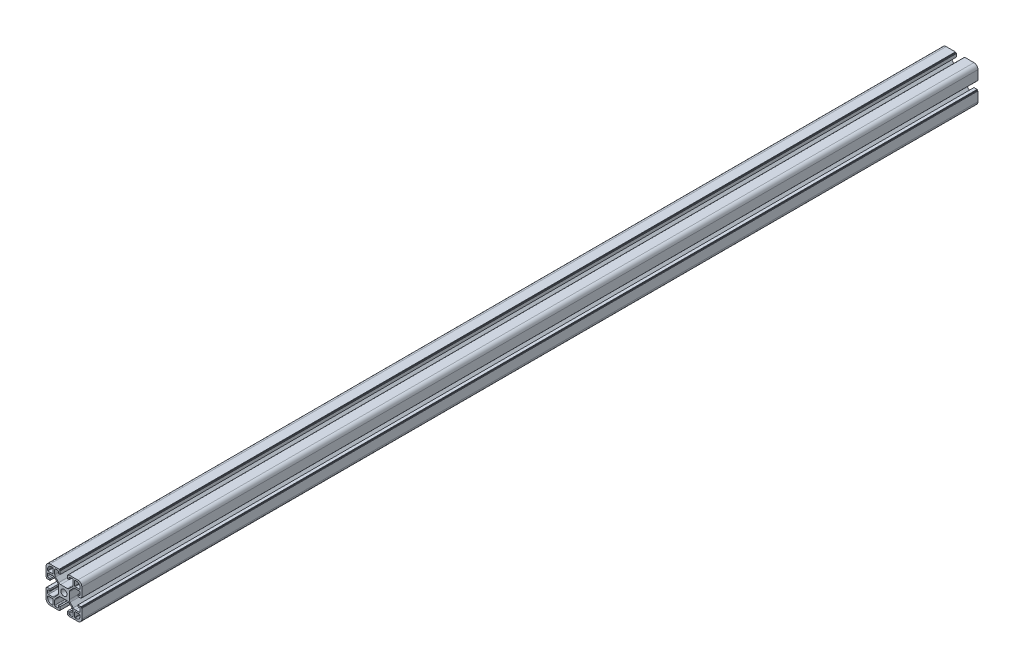
SolidWorks part; units mm, degrees
ref_plane "Front Plane" through (0, 0, 0) normal (0, 0, 1) x (1, 0, 0)
ref_plane "Top Plane" through (0, 0, 0) normal (0, 1, 0) x (1, 0, 0)
ref_plane "Right Plane" through (0, 0, 0) normal (1, 0, 0) x (0, 0, -1)
sketch "Sketch1" plane through (0, 0, 0) normal (0, 0, 1) x (1, 0, 0)
  line L0 (84.1702, 31.7204) -> (84.1702, 42.1204)
  line L1 (44.1702, 62.7204) -> (44.1702, 52.3204)
  line L2 (48.6702, 27.2204) -> (59.0702, 27.2204)
  line L3 (79.6702, 67.2204) -> (69.4702, 67.2204)
  line L4 (84.1702, 52.3204) -> (84.1702, 62.7204)
  line L5 (58.8702, 67.2204) -> (48.6702, 67.2204)
  line L6 (44.1702, 42.1204) -> (44.1702, 31.7204)
  line L7 (69.2702, 27.2204) -> (79.6702, 27.2204)
  line L10 (44.1702, 42.1204) -> (44.7702, 42.1204)
  line L11 (44.9702, 42.3204) -> (44.9702, 42.9204)
  line L12 (48.6702, 43.1204) -> (45.1702, 43.1204)
  line L13 (48.6702, 41.3204) -> (48.6702, 43.1204)
  line L14 (46.9702, 41.3204) -> (48.6702, 41.3204)
  line L15 (45.9702, 37.9704) -> (45.9702, 40.3204)
  line L16 (51.6169, 36.9704) -> (46.9702, 36.9704)
  line L17 (57.2915, 41.4024) -> (53.7382, 37.8491)
  line L18 (58.1702, 50.9171) -> (58.1702, 43.5237)
  line L19 (53.7382, 56.5917) -> (57.2915, 53.0384)
  line L20 (46.9702, 57.4704) -> (51.6169, 57.4704)
  line L21 (45.9702, 54.1204) -> (45.9702, 56.4704)
  line L22 (48.6702, 53.1204) -> (46.9702, 53.1204)
  line L23 (48.6702, 51.3204) -> (48.6702, 53.1204)
  line L24 (45.1702, 51.3204) -> (48.6702, 51.3204)
  line L25 (44.9702, 51.5204) -> (44.9702, 52.1204)
  line L26 (44.7702, 52.3204) -> (44.1702, 52.3204)
  line L29 (59.0702, 67.0204) -> (59.0702, 66.6204)
  line L30 (59.2702, 66.4204) -> (59.8702, 66.4204)
  line L31 (60.0702, 62.7204) -> (60.0702, 66.2204)
  line L32 (58.2702, 62.7204) -> (60.0702, 62.7204)
  line L33 (58.2702, 64.4204) -> (58.2702, 62.7204)
  line L34 (54.9202, 65.4204) -> (57.2702, 65.4204)
  line L35 (53.9202, 59.7737) -> (53.9202, 64.4204)
  line L36 (58.3522, 54.0991) -> (54.7989, 57.6524)
  line L37 (67.8669, 53.2204) -> (60.4735, 53.2204)
  line L38 (73.5415, 57.6524) -> (69.9882, 54.0991)
  line L39 (74.4202, 64.4204) -> (74.4202, 59.7737)
  line L40 (71.0702, 65.4204) -> (73.4202, 65.4204)
  line L41 (70.0702, 62.7204) -> (70.0702, 64.4204)
  line L42 (68.2702, 62.7204) -> (70.0702, 62.7204)
  line L43 (68.2702, 66.2204) -> (68.2702, 62.7204)
  line L44 (68.4702, 66.4204) -> (69.0702, 66.4204)
  line L45 (69.2702, 66.6204) -> (69.2702, 67.0204)
  line L48 (84.1702, 52.3204) -> (83.5702, 52.3204)
  line L49 (83.3702, 52.1204) -> (83.3702, 51.5204)
  line L50 (79.6702, 51.3204) -> (83.1702, 51.3204)
  line L51 (79.6702, 53.1204) -> (79.6702, 51.3204)
  line L52 (81.3702, 53.1204) -> (79.6702, 53.1204)
  line L53 (82.3702, 56.4704) -> (82.3702, 54.1204)
  line L54 (76.7235, 57.4704) -> (81.3702, 57.4704)
  line L55 (71.0489, 53.0384) -> (74.6022, 56.5917)
  line L56 (70.1702, 43.5237) -> (70.1702, 50.9171)
  line L57 (74.6022, 37.8491) -> (71.0489, 41.4024)
  line L58 (81.3702, 36.9704) -> (76.7235, 36.9704)
  line L59 (82.3702, 40.3204) -> (82.3702, 37.9704)
  line L60 (79.6702, 41.3204) -> (81.3702, 41.3204)
  line L61 (79.6702, 43.1204) -> (79.6702, 41.3204)
  line L62 (83.1702, 43.1204) -> (79.6702, 43.1204)
  line L63 (83.3702, 42.9204) -> (83.3702, 42.3204)
  line L64 (83.5702, 42.1204) -> (84.1702, 42.1204)
  line L67 (69.2702, 27.2204) -> (69.2702, 27.8204)
  line L68 (69.0702, 28.0204) -> (68.4702, 28.0204)
  line L69 (68.2702, 31.7204) -> (68.2702, 28.2204)
  line L70 (70.0702, 31.7204) -> (68.2702, 31.7204)
  line L71 (70.0702, 30.0204) -> (70.0702, 31.7204)
  line L72 (73.4202, 29.0204) -> (71.0702, 29.0204)
  line L73 (74.4202, 34.6671) -> (74.4202, 30.0204)
  line L74 (69.9882, 40.3417) -> (73.5415, 36.7884)
  line L75 (60.4735, 41.2204) -> (67.8669, 41.2204)
  line L76 (54.7989, 36.7884) -> (58.3522, 40.3417)
  line L77 (53.9202, 30.0204) -> (53.9202, 34.6671)
  line L78 (57.2702, 29.0204) -> (54.9202, 29.0204)
  line L79 (58.2702, 31.7204) -> (58.2702, 30.0204)
  line L80 (60.0702, 31.7204) -> (58.2702, 31.7204)
  line L81 (60.0702, 28.2204) -> (60.0702, 31.7204)
  line L82 (59.8702, 28.0204) -> (59.2702, 28.0204)
  line L83 (59.0702, 27.8204) -> (59.0702, 27.2204)
  line L84 (82.3702, 34.6704) -> (82.3702, 33.5204)
  line L85 (76.7202, 35.1704) -> (81.8702, 35.1704)
  line L86 (76.2202, 29.5204) -> (76.2202, 34.6704)
  line L87 (77.8702, 29.0204) -> (76.7202, 29.0204)
  line L88 (51.6202, 29.0204) -> (50.4702, 29.0204)
  line L89 (52.1202, 34.6704) -> (52.1202, 29.5204)
  line L90 (46.4702, 35.1704) -> (51.6202, 35.1704)
  line L91 (45.9702, 33.5204) -> (45.9702, 34.6704)
  line L92 (45.9702, 59.7704) -> (45.9702, 60.9204)
  line L93 (51.6202, 59.2704) -> (46.4702, 59.2704)
  line L94 (52.1202, 64.9204) -> (52.1202, 59.7704)
  line L95 (50.4702, 65.4204) -> (51.6202, 65.4204)
  line L96 (76.7202, 65.4204) -> (77.8702, 65.4204)
  line L97 (76.2202, 59.7704) -> (76.2202, 64.9204)
  line L98 (81.8702, 59.2704) -> (76.7202, 59.2704)
  line L99 (82.3702, 60.9204) -> (82.3702, 59.7704)
  arc A0 (60.7702, 47.2204) -> (67.5702, 47.2204) centre (64.1702, 47.2204) ccw
  arc A1 (44.1702, 31.7204) -> (48.6702, 27.2204) centre (48.6702, 31.7204) ccw
  arc A2 (44.7702, 42.1204) -> (44.9702, 42.3204) centre (44.7702, 42.3204) ccw
  arc A3 (45.1702, 43.1204) -> (44.9702, 42.9204) centre (45.1702, 42.9204) ccw
  arc A4 (46.9702, 41.3204) -> (45.9702, 40.3204) centre (46.9702, 40.3204) ccw
  arc A5 (45.9702, 37.9704) -> (46.9702, 36.9704) centre (46.9702, 37.9704) ccw
  arc A6 (51.6169, 36.9704) -> (53.7382, 37.8491) centre (51.6169, 39.9704) ccw
  arc A7 (57.2915, 41.4024) -> (58.1702, 43.5237) centre (55.1702, 43.5237) ccw
  arc A8 (58.1702, 50.9171) -> (57.2915, 53.0384) centre (55.1702, 50.9171) ccw
  arc A9 (53.7382, 56.5917) -> (51.6169, 57.4704) centre (51.6169, 54.4704) ccw
  arc A10 (46.9702, 57.4704) -> (45.9702, 56.4704) centre (46.9702, 56.4704) ccw
  arc A11 (45.9702, 54.1204) -> (46.9702, 53.1204) centre (46.9702, 54.1204) ccw
  arc A12 (44.9702, 51.5204) -> (45.1702, 51.3204) centre (45.1702, 51.5204) ccw
  arc A13 (44.9702, 52.1204) -> (44.7702, 52.3204) centre (44.7702, 52.1204) ccw
  arc A14 (48.6702, 67.2204) -> (44.1702, 62.7204) centre (48.6702, 62.7204) ccw
  arc A15 (59.0702, 67.0204) -> (58.8702, 67.2204) centre (58.8702, 67.0204) ccw
  arc A16 (59.0702, 66.6204) -> (59.2702, 66.4204) centre (59.2702, 66.6204) ccw
  arc A17 (60.0702, 66.2204) -> (59.8702, 66.4204) centre (59.8702, 66.2204) ccw
  arc A18 (58.2702, 64.4204) -> (57.2702, 65.4204) centre (57.2702, 64.4204) ccw
  arc A19 (54.9202, 65.4204) -> (53.9202, 64.4204) centre (54.9202, 64.4204) ccw
  arc A20 (53.9202, 59.7737) -> (54.7989, 57.6524) centre (56.9202, 59.7737) ccw
  arc A21 (58.3522, 54.0991) -> (60.4735, 53.2204) centre (60.4735, 56.2204) ccw
  arc A22 (67.8669, 53.2204) -> (69.9882, 54.0991) centre (67.8669, 56.2204) ccw
  arc A23 (73.5415, 57.6524) -> (74.4202, 59.7737) centre (71.4202, 59.7737) ccw
  arc A24 (74.4202, 64.4204) -> (73.4202, 65.4204) centre (73.4202, 64.4204) ccw
  arc A25 (71.0702, 65.4204) -> (70.0702, 64.4204) centre (71.0702, 64.4204) ccw
  arc A26 (68.4702, 66.4204) -> (68.2702, 66.2204) centre (68.4702, 66.2204) ccw
  arc A27 (69.0702, 66.4204) -> (69.2702, 66.6204) centre (69.0702, 66.6204) ccw
  arc A28 (69.4702, 67.2204) -> (69.2702, 67.0204) centre (69.4702, 67.0204) ccw
  arc A29 (84.1702, 62.7204) -> (79.6702, 67.2204) centre (79.6702, 62.7204) ccw
  arc A30 (83.5702, 52.3204) -> (83.3702, 52.1204) centre (83.5702, 52.1204) ccw
  arc A31 (83.1702, 51.3204) -> (83.3702, 51.5204) centre (83.1702, 51.5204) ccw
  arc A32 (81.3702, 53.1204) -> (82.3702, 54.1204) centre (81.3702, 54.1204) ccw
  arc A33 (82.3702, 56.4704) -> (81.3702, 57.4704) centre (81.3702, 56.4704) ccw
  arc A34 (76.7235, 57.4704) -> (74.6022, 56.5917) centre (76.7235, 54.4704) ccw
  arc A35 (71.0489, 53.0384) -> (70.1702, 50.9171) centre (73.1702, 50.9171) ccw
  arc A36 (70.1702, 43.5237) -> (71.0489, 41.4024) centre (73.1702, 43.5237) ccw
  arc A37 (74.6022, 37.8491) -> (76.7235, 36.9704) centre (76.7235, 39.9704) ccw
  arc A38 (81.3702, 36.9704) -> (82.3702, 37.9704) centre (81.3702, 37.9704) ccw
  arc A39 (82.3702, 40.3204) -> (81.3702, 41.3204) centre (81.3702, 40.3204) ccw
  arc A40 (83.3702, 42.9204) -> (83.1702, 43.1204) centre (83.1702, 42.9204) ccw
  arc A41 (83.3702, 42.3204) -> (83.5702, 42.1204) centre (83.5702, 42.3204) ccw
  arc A42 (79.6702, 27.2204) -> (84.1702, 31.7204) centre (79.6702, 31.7204) ccw
  arc A43 (69.2702, 27.8204) -> (69.0702, 28.0204) centre (69.0702, 27.8204) ccw
  arc A44 (68.2702, 28.2204) -> (68.4702, 28.0204) centre (68.4702, 28.2204) ccw
  arc A45 (70.0702, 30.0204) -> (71.0702, 29.0204) centre (71.0702, 30.0204) ccw
  arc A46 (73.4202, 29.0204) -> (74.4202, 30.0204) centre (73.4202, 30.0204) ccw
  arc A47 (74.4202, 34.6671) -> (73.5415, 36.7884) centre (71.4202, 34.6671) ccw
  arc A48 (69.9882, 40.3417) -> (67.8669, 41.2204) centre (67.8669, 38.2204) ccw
  arc A49 (60.4735, 41.2204) -> (58.3522, 40.3417) centre (60.4735, 38.2204) ccw
  arc A50 (54.7989, 36.7884) -> (53.9202, 34.6671) centre (56.9202, 34.6671) ccw
  arc A51 (53.9202, 30.0204) -> (54.9202, 29.0204) centre (54.9202, 30.0204) ccw
  arc A52 (57.2702, 29.0204) -> (58.2702, 30.0204) centre (57.2702, 30.0204) ccw
  arc A53 (59.8702, 28.0204) -> (60.0702, 28.2204) centre (59.8702, 28.2204) ccw
  arc A54 (59.2702, 28.0204) -> (59.0702, 27.8204) centre (59.2702, 27.8204) ccw
  arc A55 (82.3702, 34.6704) -> (81.8702, 35.1704) centre (81.8702, 34.6704) ccw
  arc A56 (76.7202, 35.1704) -> (76.2202, 34.6704) centre (76.7202, 34.6704) ccw
  arc A57 (76.2202, 29.5204) -> (76.7202, 29.0204) centre (76.7202, 29.5204) ccw
  arc A58 (77.8702, 29.0204) -> (82.3702, 33.5204) centre (77.8702, 33.5204) ccw
  arc A59 (51.6202, 29.0204) -> (52.1202, 29.5204) centre (51.6202, 29.5204) ccw
  arc A60 (52.1202, 34.6704) -> (51.6202, 35.1704) centre (51.6202, 34.6704) ccw
  arc A61 (46.4702, 35.1704) -> (45.9702, 34.6704) centre (46.4702, 34.6704) ccw
  arc A62 (45.9702, 33.5204) -> (50.4702, 29.0204) centre (50.4702, 33.5204) ccw
  arc A63 (45.9702, 59.7704) -> (46.4702, 59.2704) centre (46.4702, 59.7704) ccw
  arc A64 (51.6202, 59.2704) -> (52.1202, 59.7704) centre (51.6202, 59.7704) ccw
  arc A65 (52.1202, 64.9204) -> (51.6202, 65.4204) centre (51.6202, 64.9204) ccw
  arc A66 (50.4702, 65.4204) -> (45.9702, 60.9204) centre (50.4702, 60.9204) ccw
  arc A67 (76.7202, 65.4204) -> (76.2202, 64.9204) centre (76.7202, 64.9204) ccw
  arc A68 (76.2202, 59.7704) -> (76.7202, 59.2704) centre (76.7202, 59.7704) ccw
  arc A69 (81.8702, 59.2704) -> (82.3702, 59.7704) centre (81.8702, 59.7704) ccw
  arc A70 (82.3702, 60.9204) -> (77.8702, 65.4204) centre (77.8702, 60.9204) ccw
  arc A71 (67.5702, 47.2204) -> (60.7702, 47.2204) centre (64.1702, 47.2204) ccw
extrude "Boss-Extrude1" add sketch "Sketch1" along normal blind 1000
